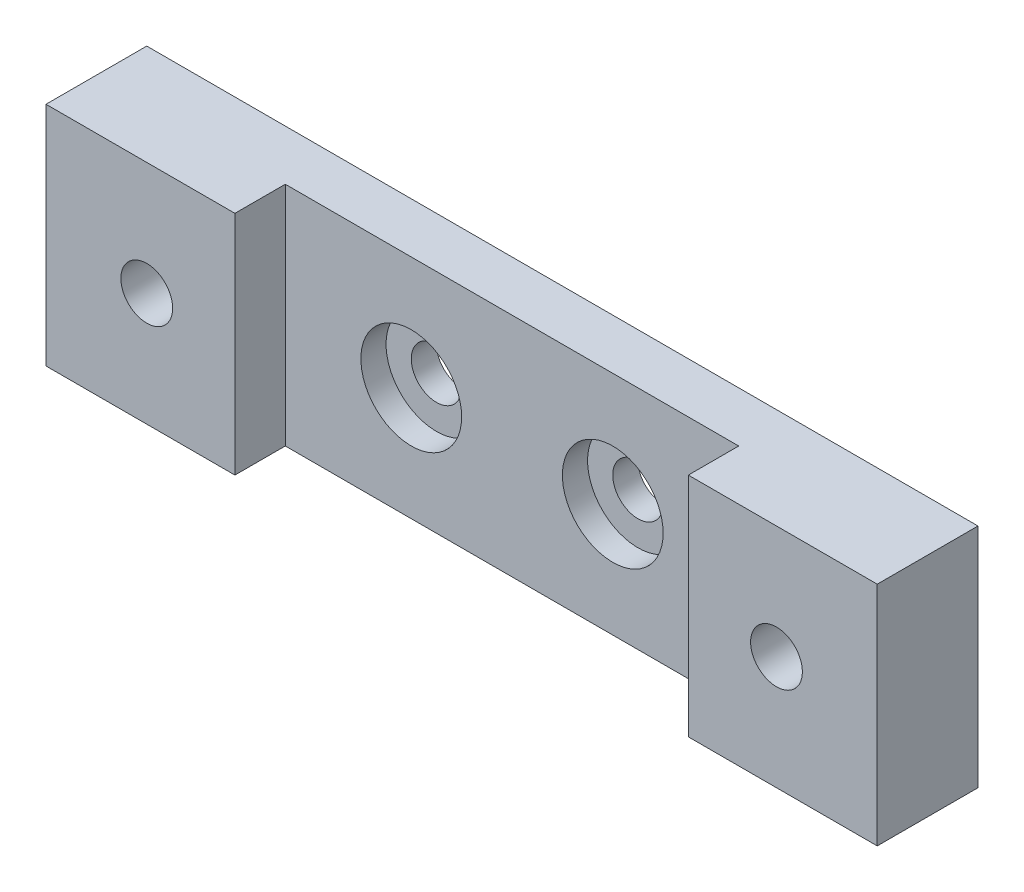
SolidWorks part; units mm, degrees
ref_plane "Front Plane" through (0, 0, 0) normal (0, 0, 1) x (1, 0, 0)
ref_plane "Top Plane" through (0, 0, 0) normal (0, 1, 0) x (1, 0, 0)
ref_plane "Right Plane" through (0, 0, 0) normal (1, 0, 0) x (0, 0, -1)
sketch "Sketch1" plane through (0, 0, 0) normal (0, 1, 0) x (1, 0, 0)
  line L0 (-52.3875, 0) -> (52.3875, 0)
  line L1 (52.3875, 0) -> (52.3875, -12.7)
  line L2 (52.3875, -12.7) -> (28.575, -12.7)
  line L3 (28.575, -12.7) -> (28.575, -6.35)
  line L4 (28.575, -6.35) -> (-28.575, -6.35)
  line L5 (-28.575, -6.35) -> (-28.575, -12.7)
  line L6 (-28.575, -12.7) -> (-52.3875, -12.7)
  line L7 (-52.3875, -12.7) -> (-52.3875, 0)
  point P7 (0, 0)
  point P10 (0, -6.35)
  dimension "D1" = 104.775
  dimension "D2" = 12.7
  dimension "D3" = 57.15
  dimension "D4" = 6.35
extrude "Boss-Extrude1" add sketch "Sketch1" along normal blind 28.575
hole_wizard "Hole1" positions "Sketch2" profile "Sketch3" legacy end condition through all
sketch "Sketch2" plane through (0, 0, 6.35) normal (0, 0, -1) x (-1, 0, 0)
  line L0 (-12.7, 14.2875) -> (12.7, 14.2875) construction
  line L2 (-52.3875, 28.575) -> (-52.3875, 0) construction
  point P0 (-12.7, 14.2875)
  point P2 (12.7, 14.2875)
  point P13 (0, 14.2875)
  point P18 (-52.3875, 14.2875)
  dimension "D1" = 25.4
sketch "Sketch3" plane through (12.7, 14.2875, 6.35) normal (1, 0, 0) x (0, -1, 0)
  line L0 (0, 0) -> (0, 8.2577)
  line L1 (0, 8.2577) -> (3.175, 6.35)
  line L2 (3.175, 6.35) -> (3.175, 3.175)
  line L3 (3.175, 3.175) -> (6.35, 3.175)
  line L4 (6.35, 0) -> (0, 0)
  line L5 (0, -11.3109) -> (0, 121.1557) construction
  line L6 (0, 8.2577) -> (-3.175, 6.35) construction
  line L7 (6.35, 3.175) -> (6.35, 0)
  dimension "Depth" = 6.35
  dimension "Drill Angle" = 118
  dimension "Diameter" = 6.35
  dimension "C-Bore Diameter" = 12.7
  dimension "C-Bore Depth" = 3.175
hole_wizard "5/16-18 Tapped Hole1" positions "Sketch6" profile "Sketch5" tap size "5/16-18" standard "ANSI Inch" end condition through all
sketch "Sketch6" plane through (0, 0, 12.7) normal (0, 0, 1) x (1, 0, 0)
  line L0 (-52.3875, 28.575) -> (-52.3875, 0) construction
  line L3 (52.3875, 28.575) -> (52.3875, 0) construction
  line L4 (-28.575, 28.575) -> (28.575, 28.575) construction
  point P0 (-39.6875, 14.2875)
  point P2 (39.6875, 14.2875)
  point P8 (-52.3875, 14.2875)
  point P20 (52.3875, 14.2875)
  point P23 (0, 28.575)
  dimension "D1" = 79.375
  dimension "D2" = 39.6875
sketch "Sketch5" plane through (-39.6875, 14.2875, 12.7) normal (1, 0, 0) x (0, -1, 0)
  line L0 (0, 0) -> (0, 12.7)
  line L1 (0, 12.7) -> (3.2639, 12.7)
  line L2 (3.2639, 12.7) -> (3.2639, 0)
  line L5 (3.2639, 0) -> (0, 0)
  line L11 (0, -6.35) -> (0, 107.95) construction
  dimension "Thru Tap Drill Dia." = 6.5278
  dimension "Thru Tap Drill Depth" = 12.7
cosmetic thread "Hole Thread1" parameters "D2"=7.9375
cosmetic thread "Hole Thread2" parameters "D2"=7.9375
equation "\"D2@Sketch6\"=\"D1@Sketch6\"/2"
